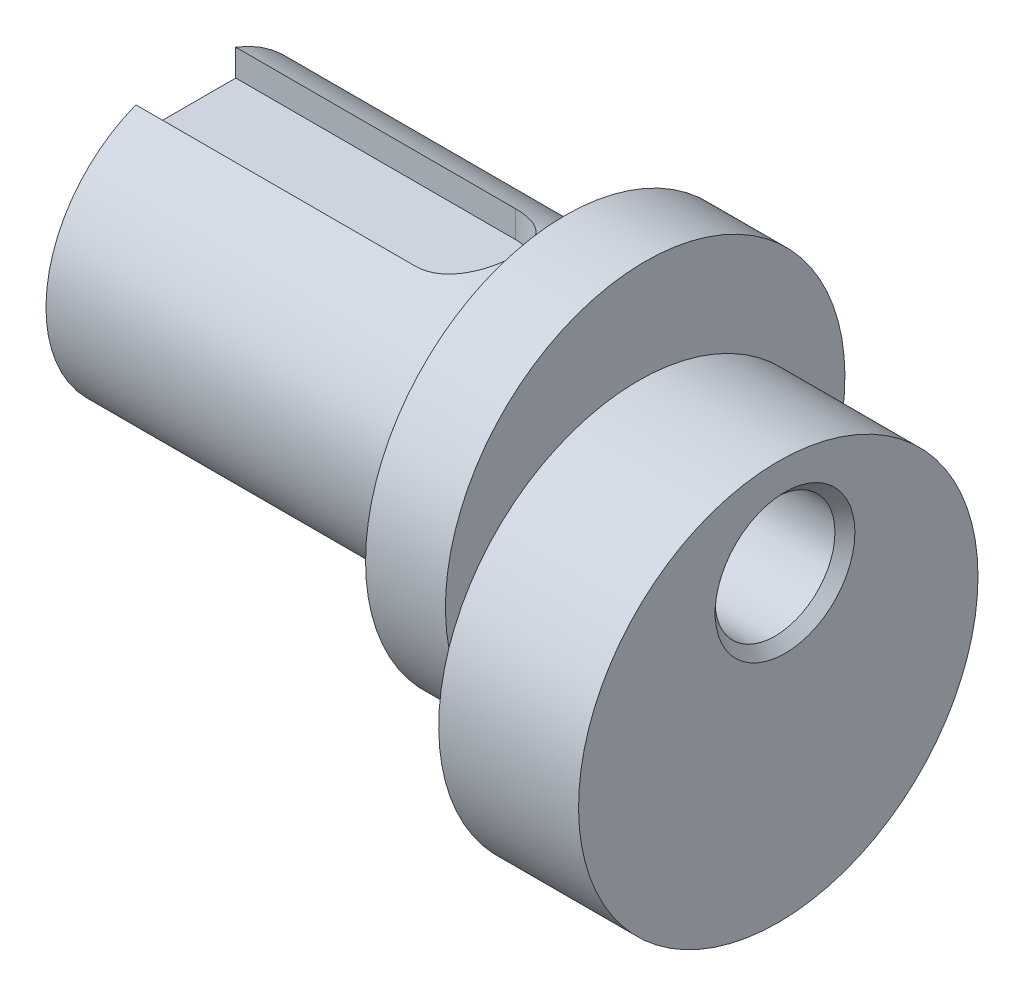
SolidWorks part; units mm, degrees
ref_plane "Front Plane" through (0, 0, 0) normal (0, 0, 1) x (1, 0, 0)
ref_plane "Top Plane" through (0, 0, 0) normal (0, 1, 0) x (1, 0, 0)
ref_plane "Right Plane" through (0, 0, 0) normal (1, 0, 0) x (0, 0, -1)
sketch "Sketch1" plane through (0, 0, 0) normal (1, 0, 0) x (0, 0, -1)
  circle A0 centre (0, 0) radius 10
extrude "Boss-Extrude1" add sketch "Sketch1" along normal blind 7
sketch "Sketch2" plane through (0, 0, 0) normal (-1, 0, 0) x (0, 0, 1)
  circle A0 centre (-0.3365, 5) radius 10
  dimension "D2" = 20
  dimension "D1" = 5
extrude "Boss-Extrude2" add sketch "Sketch2" along normal blind 4
sketch "Sketch3" plane through (-4, 0, 0) normal (-1, 0, 0) x (0, 0, 1)
  circle A0 centre (-0.3365, 5) radius 7
extrude "Boss-Extrude3" add sketch "Sketch3" along normal blind 19
sketch "Sketch4" plane through (-23, 0, 0) normal (-1, 0, 0) x (0, 0, 1)
  circle A0 centre (-0.3365, 5) radius 3
extrude "Cut-Extrude1" cut sketch "Sketch4" against normal through all
chamfer "Chamfer1" distance 0.5 angle 45 2 edges at (7, 5, 2.6635) (-23, 5, 2.6635)
sketch "Sketch5" plane through (0, 0, 0) normal (0, 1, 0) x (1, 0, 0)
  line L1 (-23, 7.3365) -> (-23, -6.6635) construction
  line L3 (-9, 2.8365) -> (-26.9868, 2.8365)
  line L5 (-9, -2.1635) -> (-26.9868, -2.1635)
  line L6 (-26.9868, 2.8365) -> (-26.9868, -2.1635)
  arc A0 (-9, 2.8365) -> (-9, -2.1635) centre (-9, 0.3365) cw
  dimension "D1" = 14
  dimension "D2" = 5
extrude "Cut-Extrude2" cut sketch "Sketch5" along normal through all from offset 10.2
